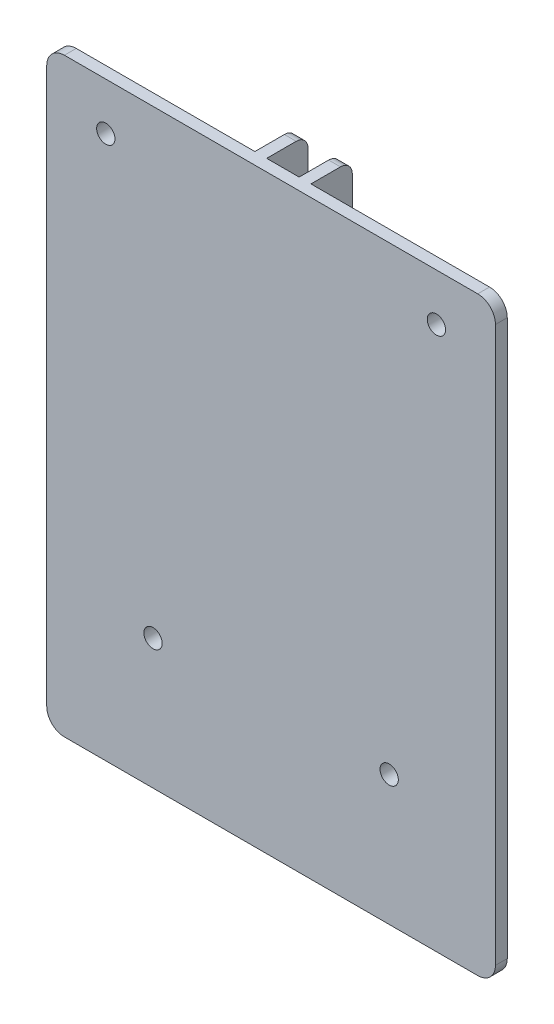
SolidWorks part; units mm, degrees
ref_plane "Plan de face" through (0, 0, 0) normal (0, 0, 1) x (1, 0, 0)
ref_plane "Plan de dessus" through (0, 0, 0) normal (0, 1, 0) x (1, 0, 0)
ref_plane "Plan de droite" through (0, 0, 0) normal (1, 0, 0) x (0, 0, -1)
sketch "Esquisse1" plane through (0, 0, 0) normal (0, 0, 1) x (1, 0, 0)
  line L1 (0, 0) -> (76, 0)
  line L2 (0, 0) -> (0, 100)
  line L3 (0, 100) -> (76, 100)
  line L4 (76, 0) -> (76, 100)
extrude "Boss.-Extru.1" add sketch "Esquisse1" along normal blind 9
sketch "Esquisse2" plane through (0, 0, 0) normal (0, 0, -1) x (-1, 0, 0)
  line L1 (-33.25, 100) -> (0, 100)
  line L2 (-33.25, 100) -> (-33.25, 0)
  line L3 (-33.25, 0) -> (0, 0)
  line L4 (0, 100) -> (0, 0)
  line L5 (-76, 100) -> (-42.75, 100)
  line L6 (-76, 100) -> (-76, 0)
  line L7 (-76, 0) -> (-42.75, 0)
  line L8 (-42.75, 100) -> (-42.75, 0)
  line L9 (-35.25, 100) -> (-40.75, 100)
  line L10 (-35.25, 100) -> (-35.25, 0)
  line L11 (-35.25, 0) -> (-40.75, 0)
  line L12 (-40.75, 100) -> (-40.75, 0)
extrude "Enlèv. mat.-Extru.1" cut sketch "Esquisse2" against normal blind 7
sketch "Esquisse3" plane through (42.75, 0, 0) normal (1, 0, 0) x (0, 0, -1)
  circle A0 centre (-3.5, 15) radius 1.55
  circle A1 centre (-3.5, 85) radius 1.55
  point P2 (0, 0)
  point P5 (0, 0)
extrude "Enlèv. mat.-Extru.2" cut sketch "Esquisse3" against normal through all
fillet "Congé1" radius 3 4 edges at (0, 0, 8) (76, 0, 8) (0, 100, 8) (76, 100, 8)
fillet "Congé2" radius 2 4 edges at (34.25, 0, 0) (41.75, 0, 0) (34.25, 100, 0) (41.75, 100, 0)
sketch "Esquisse9" plane through (0, 0, 7) normal (0, 0, -1) x (-1, 0, 0)
  circle A1 centre (-66, 92) radius 3
  circle A2 centre (-10, 92) radius 3
  circle A3 centre (-18, 22) radius 3
  circle A4 centre (-58, 22) radius 3
extrude "Boss.-Extru.2" add sketch "Esquisse9" along normal blind 3
sketch "Esquisse5" plane through (0, 0, 7) normal (0, 0, -1) x (-1, 0, 0)
  circle A0 centre (-66, 92) radius 1.55
  circle A1 centre (-58, 22) radius 1.55
  circle A2 centre (-18, 22) radius 1.55
  circle A3 centre (-10, 92) radius 1.55
extrude "Enlèv. mat.-Extru.4" cut sketch "Esquisse5" against normal through all both and the other way through all
